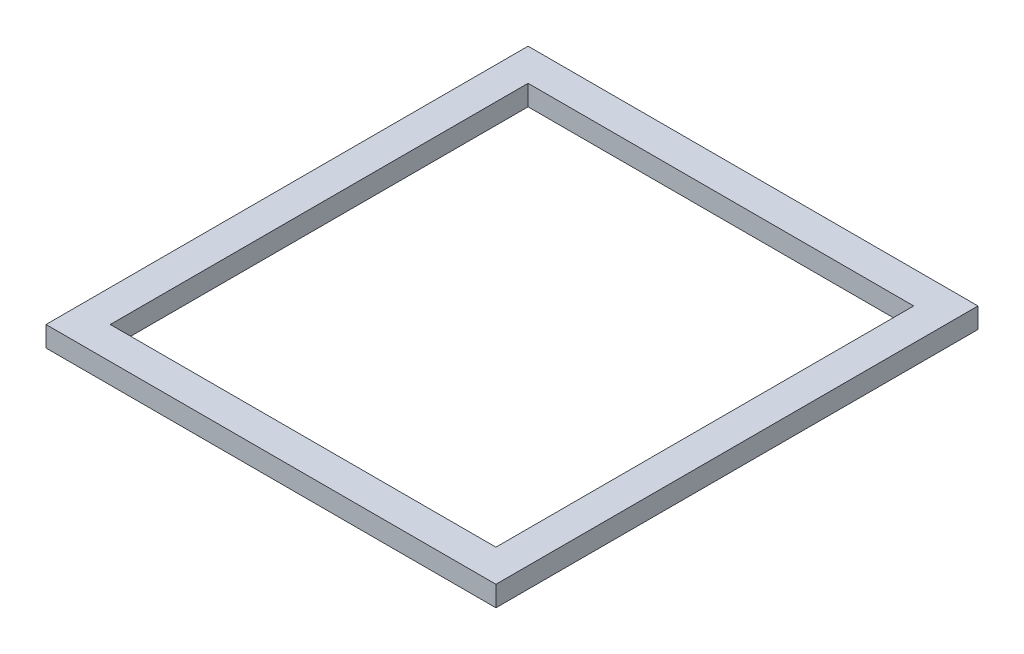
SolidWorks part; units mm, degrees
ref_plane "Front Plane" through (0, 0, 0) normal (0, 0, 1) x (1, 0, 0)
ref_plane "Top Plane" through (0, 0, 0) normal (0, 1, 0) x (1, 0, 0)
ref_plane "Right Plane" through (0, 0, 0) normal (1, 0, 0) x (0, 0, -1)
sketch "Sketch1" plane through (0, 0, 0) normal (0, 1, 0) x (1, 0, 0)
  line L1 (0, 0) -> (120, 0)
  line L2 (0, 0) -> (0, 130)
  line L3 (0, 130) -> (120, 130)
  line L4 (120, 0) -> (120, 130)
  line L5 (-10, 140) -> (130, 140)
  line L6 (-10, 140) -> (-10, -10)
  line L7 (-10, -10) -> (130, -10)
  line L8 (130, 140) -> (130, -10)
  point P4 (60, 140)
  point P10 (60, 130)
  point P11 (130, 65)
  point P12 (120, 65)
  dimension "D1" = 130
  dimension "D2" = 120
  dimension "D3" = 140
  dimension "D4" = 150
extrude "Boss-Extrude1" add sketch "Sketch1" along normal blind 6.35
sketch "Sketch2" plane through (0, 6.35, 0) normal (0, 1, 0) x (1, 0, 0)
  line L0 (33, 130) -> (33, 140)
  line L1 (33, 0) -> (33, -10)
  line L2 (130, 140) -> (-10, 140) construction
  line L3 (120, 130) -> (0, 130) construction
  line L5 (0, 130) -> (0, 0) construction
  line L6 (-10, -10) -> (130, -10) construction
  line L7 (0, 0) -> (120, 0) construction
  point P4 (0, 0)
  point P7 (0, 0)
  point P8 (6.5898, 121.196)
  point P9 (6.1497, 135)
  point P10 (0, 0)
  point P15 (0, 0)
  point P18 (0, 0)
  dimension "D1" = 33
